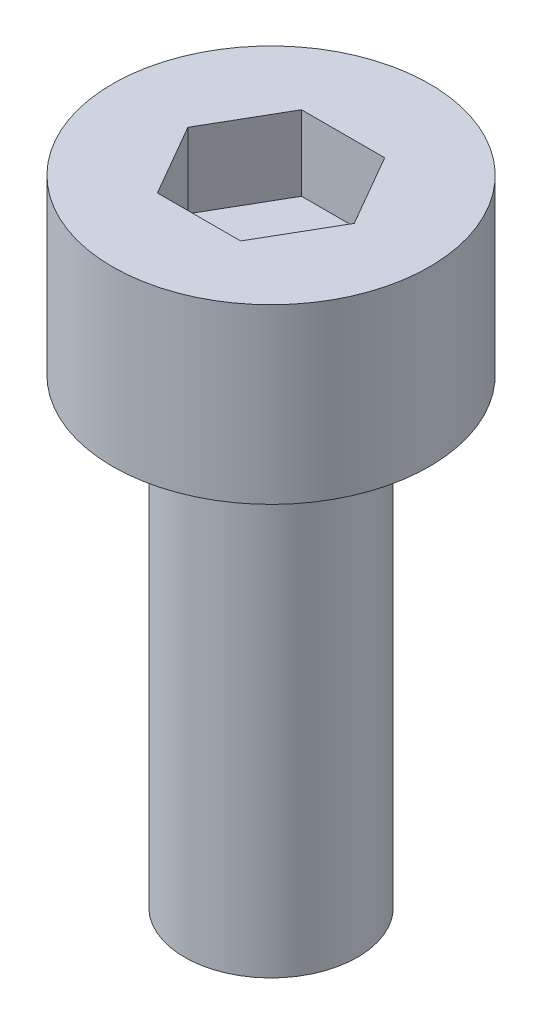
SolidWorks part; units mm, degrees
material "AISI 304"
ref_plane "前视基准面" through (0, 0, 0) normal (0, 0, 1) x (1, 0, 0)
ref_plane "上视基准面" through (0, 0, 0) normal (0, 1, 0) x (1, 0, 0)
ref_plane "右视基准面" through (0, 0, 0) normal (1, 0, 0) x (0, 0, -1)
sketch "草图1" plane through (0, 0, 0) normal (0, 1, 0) x (1, 0, 0)
  circle A0 centre (0, 0) radius 2.75
  dimension "D1" = 5.5
extrude "杯头" add sketch "草图1" along normal blind 3
sketch "草图2" plane through (0, 3, 0) normal (0, 1, 0) x (1, 0, 0)
  line L1 (1.4434, 0) -> (0.7217, 1.25)
  line L2 (0.7217, 1.25) -> (-0.7217, 1.25)
  line L3 (-0.7217, 1.25) -> (-1.4434, 0)
  line L4 (-1.4434, 0) -> (-0.7217, -1.25)
  line L5 (-0.7217, -1.25) -> (0.7217, -1.25)
  line L6 (0.7217, -1.25) -> (1.4434, 0)
  circle A0 centre (0, 0) radius 1.25 construction
  dimension "D1" = 2.5
extrude "内六角口" cut sketch "草图2" against normal blind 1.3
sketch "草图3" plane through (0, 0, 0) normal (0, -1, 0) x (1, 0, 0)
  circle A0 centre (0, 0) radius 1.5
  dimension "D1" = 3
extrude "螺纹长" add sketch "草图3" along normal blind 8
